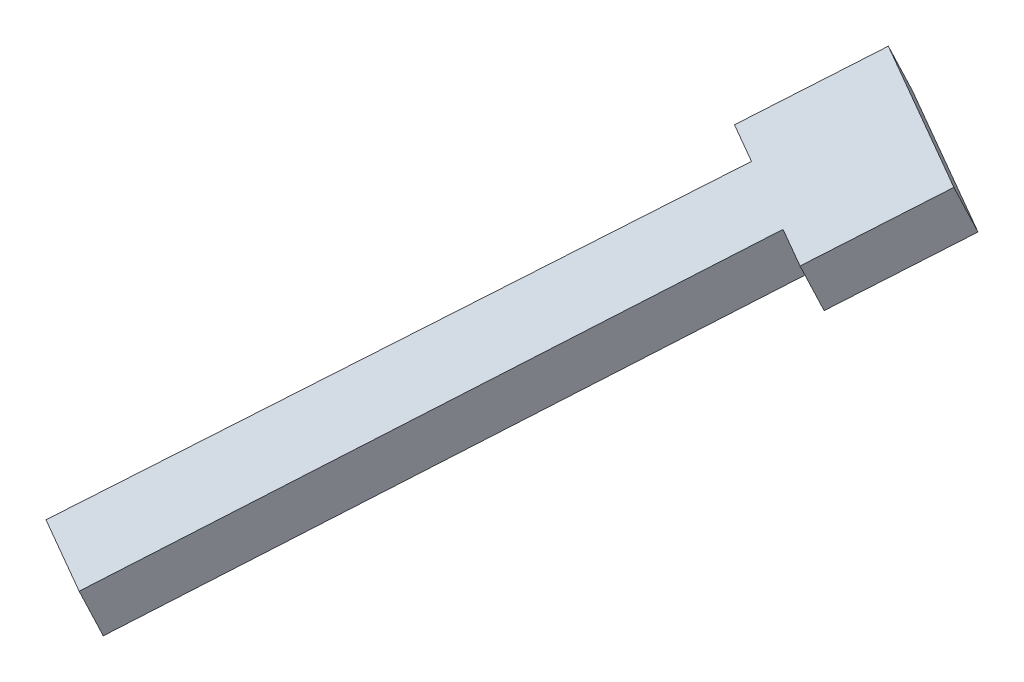
SolidWorks part; units mm, degrees
ref_plane "Front Plane" through (0, 0, 0) normal (0, 0, 1) x (1, 0, 0)
ref_plane "Top Plane" through (0, 0, 0) normal (0, 1, 0) x (1, 0, 0)
ref_plane "Right Plane" through (0, 0, 0) normal (1, 0, 0) x (0, 0, -1)
sketch "Sketch1" plane through (-15.8648, 0, -9.1596) normal (0.866, 0, 0.5) x (0.5, 0, -0.866)
  line L0 (-250.8979, -141.4858) -> (-306.1863, -164.7923)
  line L1 (-268.5551, -99.5986) -> (-250.8785, -141.5319) construction
  line L2 (-316.3992, -140.5649) -> (-295.9734, -189.0196) construction
  line L3 (-306.1863, -164.7923) -> (-304.6326, -168.4781)
  line L4 (-304.6326, -168.4781) -> (-249.3441, -145.1717)
  line L5 (-249.3441, -145.1717) -> (-250.8979, -141.4858)
  dimension "D1" = 4
extrude "Boss-Extrude1" add sketch "Sketch1" against normal up to surface (15.75 mm away)
sketch "Sketch2" plane through (6.3931, -30.3318, -11.0731) normal (-0.1942, 0.9215, 0.3364) x (0.981, 0.1824, 0.0666)
  line L0 (-192.6596, -289.5963) -> (-189.2229, -291.4247)
  line L1 (-192.6596, -289.5963) -> (-178.7549, -296.9938) construction
  line L2 (-189.2229, -291.4247) -> (-165.9228, -248.0368)
  line L3 (-165.9228, -248.0368) -> (-175.3868, -243.0019)
  line L4 (-175.3868, -243.0019) -> (-198.5176, -286.4798)
  line L5 (-198.5176, -286.4798) -> (-192.6596, -289.5963)
  line L6 (-185.7073, -293.2951) -> (-168.5272, -261.0025) construction
  line L7 (-149.7661, -256.6324) -> (-172.897, -300.1103)
  line L8 (-159.2301, -251.5974) -> (-149.7661, -256.6324)
  line L9 (-182.1917, -295.1654) -> (-159.2301, -251.5974)
  line L10 (-172.897, -300.1103) -> (-178.7549, -296.9938)
  line L11 (-178.7549, -296.9938) -> (-182.1917, -295.1654)
  line L12 (-154.9001, -242.5739) -> (-160.8592, -239.4036) construction
  point P16 (0, 0)
  point P17 (0, 0)
  dimension "D1" = 10
extrude "Cut-Extrude1" cut sketch "Sketch2" against normal through all
